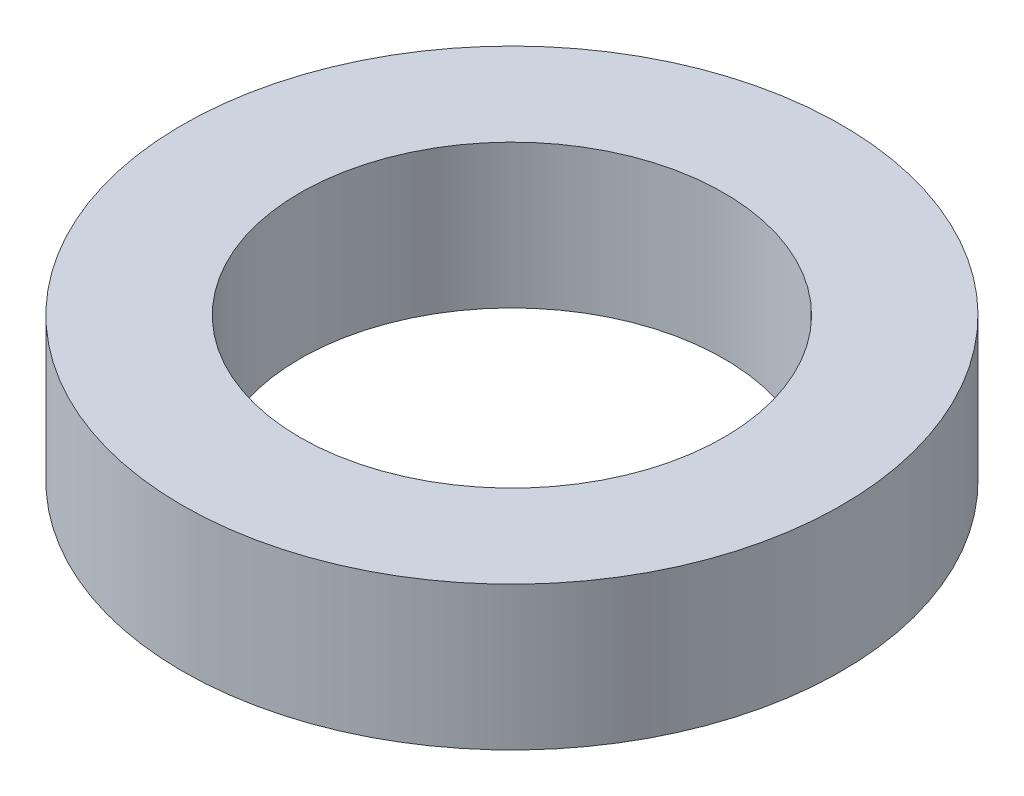
SolidWorks part; units mm, degrees
material "Custom Plastic2"
ref_plane "Front Plane" through (0, 0, 0) normal (0, 0, 1) x (1, 0, 0)
ref_plane "Top Plane" through (0, 0, 0) normal (0, 1, 0) x (1, 0, 0)
ref_plane "Right Plane" through (0, 0, 0) normal (1, 0, 0) x (0, 0, -1)
sketch "Sketch1" plane through (0, 0, 0) normal (0, 1, 0) x (1, 0, 0)
  circle A0 centre (0, 0) radius 28
  dimension "D1" = 56
extrude "Boss-Extrude1" add sketch "Sketch1" along normal blind 12.2
sketch "Sketch2" plane through (0, 0, 0) normal (0, 1, 0) x (1, 0, 0)
  circle A0 centre (0, 0) radius 18.0025
  dimension "D1" = 36.005
extrude "Cut-Extrude1" cut sketch "Sketch2" along normal through all
